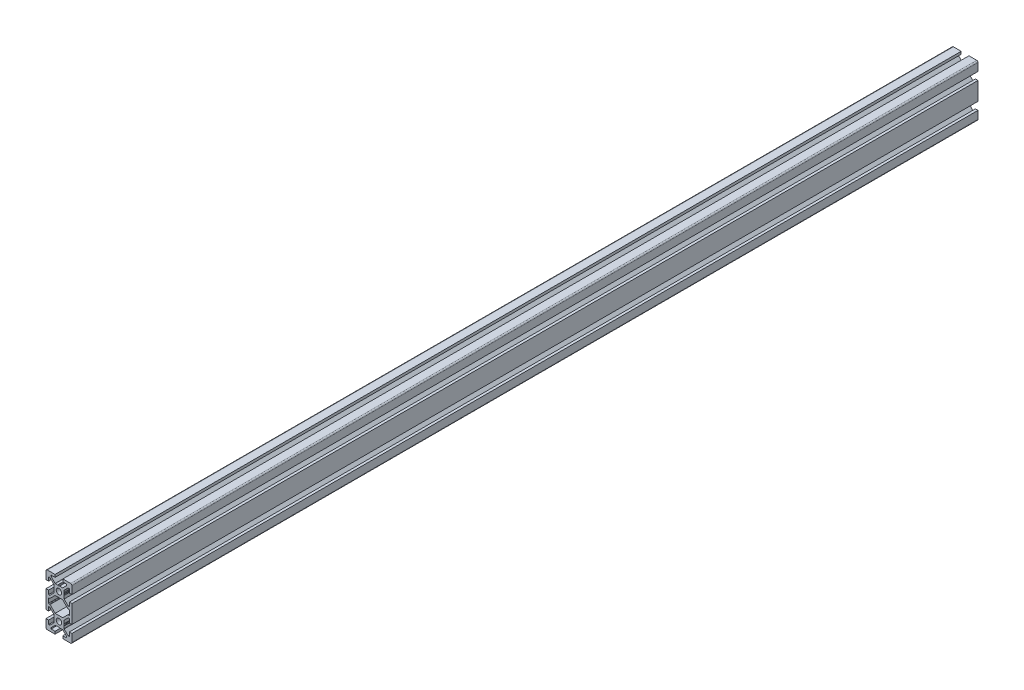
SolidWorks part; units mm, degrees
material "1060 Alloy"
ref_plane "Front Plane" through (0, 0, 0) normal (0, 0, 1) x (1, 0, 0)
ref_plane "Top Plane" through (0, 0, 0) normal (0, 1, 0) x (1, 0, 0)
ref_plane "Right Plane" through (0, 0, 0) normal (1, 0, 0) x (0, 0, -1)
ref_plane "Plane1" through (0, 0, -600) normal (0, 0, -1) x (-1, 0, 0)
sketch "Sketch1" plane through (0, 0, -600) normal (0, 0, -1) x (-1, 0, 0)
  line L0 (8, 1.7) -> (8, -1.7)
  line L1 (7.7, -2) -> (7.0636, -2)
  line L2 (6.8515, -2.0879) -> (2.9393, -6)
  line L3 (2.9393, -6) -> (-2.9393, -6)
  line L4 (-2.9393, -6) -> (-6.8515, -2.0879)
  line L5 (-7.0636, -2) -> (-7.7, -2)
  line L6 (-8, -1.7) -> (-8, 1.7)
  line L7 (-7.7, 2) -> (-7.0636, 2)
  line L8 (-6.8515, 2.0879) -> (-2.9393, 6)
  line L9 (-2.9393, 6) -> (2.9393, 6)
  line L10 (2.9393, 6) -> (6.8515, 2.0879)
  line L11 (7.0636, 2) -> (7.7, 2)
  line L12 (10, -7) -> (10, 7)
  line L13 (10, 7) -> (8, 7)
  line L14 (8, 7) -> (8, 4)
  line L15 (8, 4) -> (7.0607, 4)
  line L16 (7.0607, 4) -> (4, 7.0607)
  line L17 (4, 7.0607) -> (4, 7.5)
  line L18 (4, 7.5) -> (3.751, 8.7811)
  line L19 (3.751, 8.7811) -> (3.933, 9.0964)
  line L20 (3.933, 9.5964) -> (3.7, 10)
  line L21 (3.7, 10) -> (3.933, 10.4036)
  line L22 (4, 10.6536) -> (4, 12.9393)
  line L23 (4, 12.9393) -> (7.0607, 16)
  line L24 (7.0607, 16) -> (8, 16)
  line L25 (8, 16) -> (8, 13)
  line L26 (8, 13) -> (10, 13)
  line L27 (10, 13) -> (10, 19)
  line L28 (9, 20) -> (3, 20)
  line L29 (3, 20) -> (3, 18)
  line L30 (3, 18) -> (6, 18)
  line L31 (6, 18) -> (6, 17.0607)
  line L32 (6, 17.0607) -> (2.9393, 14)
  line L33 (2.9393, 14) -> (2.5, 14)
  line L34 (2.5, 14) -> (1.2189, 13.751)
  line L35 (1.2189, 13.751) -> (0.9036, 13.933)
  line L36 (0.4036, 13.933) -> (0, 13.7)
  line L37 (0, 13.7) -> (-0.4036, 13.933)
  line L38 (-0.6536, 14) -> (-2.9393, 14)
  line L39 (-2.9393, 14) -> (-6, 17.0607)
  line L40 (-6, 17.0607) -> (-6, 18)
  line L41 (-6, 18) -> (-3, 18)
  line L42 (-3, 18) -> (-3, 20)
  line L43 (-3, 20) -> (-9, 20)
  line L44 (-10, 19) -> (-10, 13)
  line L45 (-10, 13) -> (-8, 13)
  line L46 (-8, 13) -> (-8, 16)
  line L47 (-8, 16) -> (-7.0607, 16)
  line L48 (-7.0607, 16) -> (-4, 12.9393)
  line L49 (-4, 12.9393) -> (-4, 12.5)
  line L50 (-4, 12.5) -> (-3.751, 11.2189)
  line L51 (-3.751, 11.2189) -> (-3.933, 10.9036)
  line L52 (-3.933, 10.4036) -> (-3.7, 10)
  line L53 (-3.7, 10) -> (-3.933, 9.5964)
  line L54 (-4, 9.3464) -> (-4, 7.0607)
  line L55 (-4, 7.0607) -> (-7.0607, 4)
  line L56 (-7.0607, 4) -> (-8, 4)
  line L57 (-8, 4) -> (-8, 7)
  line L58 (-8, 7) -> (-10, 7)
  line L59 (-10, 7) -> (-10, -7)
  line L60 (-10, -7) -> (-8, -7)
  line L61 (-8, -7) -> (-8, -4)
  line L62 (-8, -4) -> (-7.0607, -4)
  line L63 (-7.0607, -4) -> (-4, -7.0607)
  line L64 (-4, -7.0607) -> (-4, -9.3464)
  line L65 (-3.933, -9.5964) -> (-3.7, -10)
  line L66 (-3.7, -10) -> (-3.933, -10.4036)
  line L67 (-3.933, -10.9036) -> (-3.751, -11.2189)
  line L68 (-3.751, -11.2189) -> (-4, -12.5)
  line L69 (-4, -12.5) -> (-4, -12.9393)
  line L70 (-4, -12.9393) -> (-7.0607, -16)
  line L71 (-7.0607, -16) -> (-8, -16)
  line L72 (-8, -16) -> (-8, -13)
  line L73 (-8, -13) -> (-10, -13)
  line L74 (-10, -13) -> (-10, -19)
  line L75 (-9, -20) -> (-3, -20)
  line L76 (-3, -20) -> (-3, -18)
  line L77 (-3, -18) -> (-6, -18)
  line L78 (-6, -18) -> (-6, -17.0607)
  line L79 (-6, -17.0607) -> (-2.9393, -14)
  line L80 (-2.9393, -14) -> (-0.6536, -14)
  line L81 (-0.4036, -13.933) -> (0, -13.7)
  line L82 (0, -13.7) -> (0.4036, -13.933)
  line L83 (0.9036, -13.933) -> (1.2189, -13.751)
  line L84 (1.2189, -13.751) -> (2.5, -14)
  line L85 (2.5, -14) -> (2.9393, -14)
  line L86 (2.9393, -14) -> (6, -17.0607)
  line L87 (6, -17.0607) -> (6, -18)
  line L88 (6, -18) -> (3, -18)
  line L89 (3, -18) -> (3, -20)
  line L90 (3, -20) -> (9, -20)
  line L91 (10, -19) -> (10, -13)
  line L92 (10, -13) -> (8, -13)
  line L93 (8, -13) -> (8, -16)
  line L94 (8, -16) -> (7.0607, -16)
  line L95 (7.0607, -16) -> (4, -12.9393)
  line L96 (4, -12.9393) -> (4, -10.6536)
  line L97 (3.933, -10.4036) -> (3.7, -10)
  line L98 (3.7, -10) -> (3.933, -9.5964)
  line L99 (3.933, -9.0964) -> (3.751, -8.7811)
  line L100 (3.751, -8.7811) -> (4, -7.5)
  line L101 (4, -7.5) -> (4, -7.0607)
  line L102 (4, -7.0607) -> (7.0607, -4)
  line L103 (7.0607, -4) -> (8, -4)
  line L104 (8, -4) -> (8, -7)
  line L105 (8, -7) -> (10, -7)
  circle A0 centre (0, -10) radius 2.1
  circle A1 centre (0, 10) radius 2.1
  arc A2 (7.7, 2) -> (8, 1.7) centre (7.7, 1.7) cw
  arc A3 (8, -1.7) -> (7.7, -2) centre (7.7, -1.7) cw
  arc A4 (7.0636, -2) -> (6.8515, -2.0879) centre (7.0636, -2.3) ccw
  arc A5 (-6.8515, -2.0879) -> (-7.0636, -2) centre (-7.0636, -2.3) ccw
  arc A6 (-7.7, -2) -> (-8, -1.7) centre (-7.7, -1.7) cw
  arc A7 (-8, 1.7) -> (-7.7, 2) centre (-7.7, 1.7) cw
  arc A8 (-7.0636, 2) -> (-6.8515, 2.0879) centre (-7.0636, 2.3) ccw
  arc A9 (6.8515, 2.0879) -> (7.0636, 2) centre (7.0636, 2.3) ccw
  arc A10 (3.933, 9.0964) -> (3.933, 9.5964) centre (3.5, 9.3464) ccw
  arc A11 (3.933, 10.4036) -> (4, 10.6536) centre (3.5, 10.6536) ccw
  arc A12 (10, 19) -> (9, 20) centre (9, 19) ccw
  arc A13 (0.9036, 13.933) -> (0.4036, 13.933) centre (0.6536, 13.5) ccw
  arc A14 (-0.4036, 13.933) -> (-0.6536, 14) centre (-0.6536, 13.5) ccw
  arc A15 (-9, 20) -> (-10, 19) centre (-9, 19) ccw
  arc A16 (-3.933, 10.9036) -> (-3.933, 10.4036) centre (-3.5, 10.6536) ccw
  arc A17 (-3.933, 9.5964) -> (-4, 9.3464) centre (-3.5, 9.3464) ccw
  arc A18 (-4, -9.3464) -> (-3.933, -9.5964) centre (-3.5, -9.3464) ccw
  arc A19 (-3.933, -10.4036) -> (-3.933, -10.9036) centre (-3.5, -10.6536) ccw
  arc A20 (-10, -19) -> (-9, -20) centre (-9, -19) ccw
  arc A21 (-0.6536, -14) -> (-0.4036, -13.933) centre (-0.6536, -13.5) ccw
  arc A22 (0.4036, -13.933) -> (0.9036, -13.933) centre (0.6536, -13.5) ccw
  arc A23 (9, -20) -> (10, -19) centre (9, -19) ccw
  arc A24 (4, -10.6536) -> (3.933, -10.4036) centre (3.5, -10.6536) ccw
  arc A25 (3.933, -9.5964) -> (3.933, -9.0964) centre (3.5, -9.3464) ccw
  dimension "D1" = 4.2
  dimension "D3" = 0.3
  dimension "D4" = 0.3
  dimension "D5" = 0.3
  dimension "D6" = 0.3
  dimension "D7" = 0.3
  dimension "D8" = 0.3
  dimension "D9" = 0.3
  dimension "D10" = 0.5
  dimension "D11" = 0.5
  dimension "D12" = 1
  dimension "D13" = 0.5
  dimension "D14" = 0.5
  dimension "D15" = 1
  dimension "D16" = 0.5
  dimension "D17" = 0.5
  dimension "D18" = 0.5
  dimension "D19" = 0.5
  dimension "D20" = 0.4036
  dimension "D21" = 0.5
  dimension "D22" = 0.5
  dimension "D23" = 1
  dimension "D24" = 0.5
  dimension "D25" = 0.5
  dimension "D26" = 0.4036
  dimension "D27" = 0.6536
  dimension "D28" = 0.6536
  dimension "D29" = 0.9036
  dimension "D30" = 0.9036
  dimension "D31" = 1.2189
  dimension "D32" = 1.2189
  dimension "D33" = 2.5
  dimension "D34" = 2.5
  dimension "D35" = 2.9393
  dimension "D36" = 2.9393
  dimension "D37" = 3
  dimension "D38" = 3.5
  dimension "D39" = 6
  dimension "D40" = 6.8515
  dimension "D41" = 3.7
  dimension "D42" = 3.7
  dimension "D43" = 3.751
  dimension "D44" = 3.751
  dimension "D45" = 3.933
  dimension "D46" = 3.933
  dimension "D47" = 6.8515
  dimension "D48" = 7.0607
  dimension "D49" = 7.0607
  dimension "D50" = 7.0636
  dimension "D51" = 7.0636
  dimension "D52" = 8
  dimension "D53" = 10
  dimension "D54" = 3
  dimension "D55" = 4
  dimension "D56" = 6
  dimension "D57" = 6.8515
  dimension "D58" = 6.8515
  dimension "D59" = 7.0607
  dimension "D60" = 7.0607
  dimension "D61" = 0.4036
  dimension "D62" = 0.4036
  dimension "D63" = 0.6536
  dimension "D64" = 0.6536
  dimension "D65" = 2.9393
  dimension "D66" = 2.9393
  dimension "D67" = 8
  dimension "D68" = 2
  dimension "D69" = 3.5
  dimension "D70" = 3.5
  dimension "D71" = 3.7
  dimension "D72" = 3.7
  dimension "D73" = 3.751
  dimension "D74" = 3.751
  dimension "D75" = 3.933
  dimension "D76" = 3.933
  dimension "D77" = 4
  dimension "D78" = 6
  dimension "D79" = 7
  dimension "D80" = 7.0607
  dimension "D81" = 7.0607
  dimension "D82" = 7.5
  dimension "D83" = 8.7811
  dimension "D84" = 9.0964
  dimension "D85" = 9.3464
  dimension "D86" = 9.3464
  dimension "D87" = 9.5964
  dimension "D88" = 9.5964
  dimension "D89" = 10.4036
  dimension "D90" = 12.5
  dimension "D91" = 13
  dimension "D92" = 13.5
  dimension "D93" = 13.5
  dimension "D94" = 18
  dimension "D95" = 20
  dimension "D96" = 2
  dimension "D97" = 4
  dimension "D98" = 6
  dimension "D99" = 7
  dimension "D100" = 7.0607
  dimension "D101" = 7.0607
  dimension "D102" = 7.5
  dimension "D103" = 8.7811
  dimension "D104" = 9.0964
  dimension "D105" = 9.3464
  dimension "D106" = 9.3464
  dimension "D107" = 9.5964
  dimension "D108" = 9.5964
  dimension "D109" = 10.4036
  dimension "D110" = 12.5
  dimension "D111" = 13
  dimension "D112" = 18
extrude "Boss-Extrude1" add sketch "Sketch1" against normal blind 700
sketch "Sketch2" plane through (-10, 0, 0) normal (-1, 0, 0) x (0, 0, 1)
  line L0 (100, 13) -> (100, 7) construction
  line L1 (100, 10) -> (90, 10) construction
  line L2 (100, -7) -> (100, -13) construction
  line L3 (100, -10) -> (90, -10) construction
  circle A0 centre (90, 10) radius 2
  circle A1 centre (90, -10) radius 2
  dimension "D3" = 4
  dimension "D4" = 4
  dimension "D1" = 10
  dimension "D2" = 10
extrude "Cut-Extrude1" cut sketch "Sketch2" against normal through all
ref_plane "Plane2" through (0, 0, -250) normal (0, 0, 1) x (1, 0, 0)
mirror "Mirror1" about plane through (0, 0, -250) normal (0, 0, 1) of "Cut-Extrude1"
